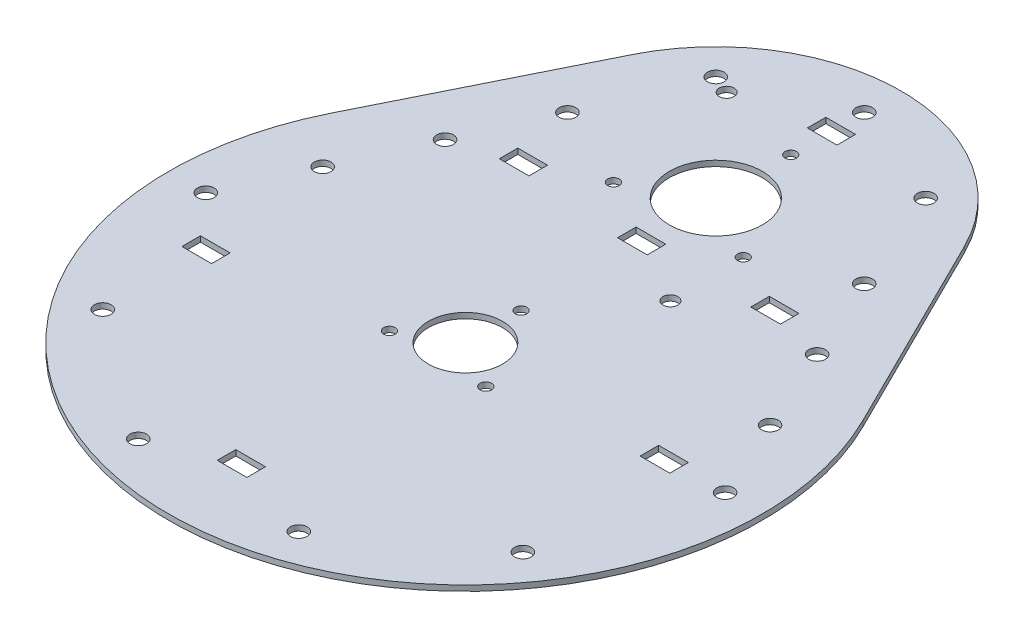
SolidWorks part; units mm, degrees
material "Plain Carbon Steel"
ref_plane "Front Plane" through (0, 0, 0) normal (0, 0, 1) x (1, 0, 0)
ref_plane "Top Plane" through (0, 0, 0) normal (0, 1, 0) x (1, 0, 0)
ref_plane "Right Plane" through (0, 0, 0) normal (1, 0, 0) x (0, 0, -1)
sketch "Sketch1" plane through (0, 0, 0) normal (0, 1, 0) x (1, 0, 0)
  line L0 (0, 67.5) -> (0, 0) construction
  line L1 (12.9904, -7.5) -> (0, 15) construction
  line L2 (0, 15) -> (-12.9904, -7.5) construction
  line L3 (-12.9904, -7.5) -> (12.9904, -7.5) construction
  line L4 (44.7903, 89.7222) -> (71.6645, 35.5556)
  line L5 (-44.7903, 89.7222) -> (-71.6645, 35.5556)
  line L6 (40, 67.5) -> (70, 0) construction
  line L7 (-4, 45) -> (4, 45)
  line L8 (-4, 45) -> (-4, 50)
  line L9 (-4, 50) -> (4, 50)
  line L10 (4, 45) -> (4, 50)
  line L11 (-4, 45) -> (4, 50) construction
  line L12 (-4, 50) -> (4, 45) construction
  line L13 (-40, 67.5) -> (-70, 0) construction
  line L14 (-5.9945, -60.9204) -> (2.0055, -60.9204)
  line L15 (-38.3758, 52.5) -> (-30.3758, 52.5)
  line L16 (-38.3758, 52.5) -> (-38.3758, 47.5)
  line L17 (-38.3758, 47.5) -> (-30.3758, 47.5)
  line L18 (-30.3758, 52.5) -> (-30.3758, 47.5)
  line L19 (-38.3758, 52.5) -> (-30.3758, 47.5) construction
  line L20 (-38.3758, 47.5) -> (-30.3758, 52.5) construction
  line L21 (30.1365, 46.7901) -> (38.1365, 46.7901)
  line L22 (30.1365, 46.7901) -> (30.1365, 51.7901)
  line L23 (30.1365, 51.7901) -> (38.1365, 51.7901)
  line L24 (38.1365, 46.7901) -> (38.1365, 51.7901)
  line L25 (30.1365, 46.7901) -> (38.1365, 51.7901) construction
  line L26 (30.1365, 51.7901) -> (38.1365, 46.7901) construction
  line L27 (-5.9945, -60.9204) -> (-5.9945, -55.9204)
  line L28 (-5.9945, -55.9204) -> (2.0055, -55.9204)
  line L29 (2.0055, -60.9204) -> (2.0055, -55.9204)
  line L30 (50.013, -2.9205) -> (58.013, -2.9205)
  line L31 (50.013, -2.9205) -> (50.013, 2.0795)
  line L32 (50.013, 2.0795) -> (58.013, 2.0795)
  line L33 (58.013, -2.9205) -> (58.013, 2.0795)
  line L34 (-60.6738, -15.7602) -> (-52.6738, -15.7602)
  line L35 (-60.6738, -15.7602) -> (-60.6738, -10.7602)
  line L36 (-60.6738, -10.7602) -> (-52.6738, -10.7602)
  line L37 (-52.6738, -15.7602) -> (-52.6738, -10.7602)
  line L38 (-4.0466, 96.2118) -> (3.9534, 96.2118)
  line L39 (-4.0466, 96.2118) -> (-4.0466, 101.2118)
  line L40 (-4.0466, 101.2118) -> (3.9534, 101.2118)
  line L41 (3.9534, 96.2118) -> (3.9534, 101.2118)
  line L43 (0, 87.7073) -> (-17.5, 57.3964) construction
  line L44 (-17.5, 57.3964) -> (17.5, 57.3964) construction
  line L45 (17.5, 57.3964) -> (0, 87.7073) construction
  circle A0 centre (0, 0) radius 10
  circle A1 centre (0, 0) radius 7.5 construction
  circle A2 centre (-12.9904, -7.5) radius 1.55
  circle A3 centre (12.9904, -7.5) radius 1.55
  circle A4 centre (0, 15) radius 1.55
  arc A6 (-71.6645, 35.5556) -> (71.6645, 35.5556) centre (0, 0) ccw
  circle A7 centre (0, 67.5) radius 12.525
  arc A8 (44.7903, 89.7222) -> (-44.7903, 89.7222) centre (0, 67.5) ccw
  circle A9 centre (0, 0) radius 35 construction
  circle A10 centre (0, 67.5) radius 15 construction
  circle A11 centre (0, 0) radius 45 construction
  circle A12 centre (0, 67.5) radius 22.5 construction
  circle A14 centre (40, 67.5) radius 2.25
  circle A15 centre (70, 0) radius 2.25
  circle A16 centre (56.6312, -41.145) radius 2.25
  circle A17 centre (21.6312, -66.574) radius 2.25
  circle A18 centre (-21.6312, -66.574) radius 2.25
  circle A19 centre (-56.6312, -41.145) radius 2.25
  circle A20 centre (-70, 0) radius 2.25
  circle A21 centre (28.2843, 95.7843) radius 2.25
  circle A22 centre (0, 107.5) radius 2.25
  circle A23 centre (-28.2843, 95.7843) radius 2.25
  circle A24 centre (-40, 67.5) radius 2.25
  circle A25 centre (-50.1535, 44.6547) radius 2.25
  circle A26 centre (-60.3069, 21.8094) radius 2.25
  circle A27 centre (50.1535, 44.6547) radius 2.25
  circle A28 centre (60.3069, 21.8094) radius 2.25
  circle A30 centre (17.8596, -30.1004) radius 2 construction
  circle A31 centre (-23.2495, 26.1622) radius 2 construction
  circle A32 centre (0, 67.5) radius 10.1036 construction
  circle A33 centre (0, 87.7073) radius 1.55
  circle A34 centre (-17.5, 57.3964) radius 1.55
  circle A35 centre (17.5, 57.3964) radius 1.55
  circle A36 centre (0, 67.5) radius 35 construction
  circle A37 centre (-23.2495, 93.6622) radius 2
  circle A38 centre (17.8596, 37.3996) radius 2
  point P11 (0, 21.0074)
  point P21 (0, 47.5)
  point P42 (0, 0)
  point P51 (0, 67.5)
  point P62 (34.1365, 49.2901)
  point P63 (-34.3758, 50)
  dimension "D1" = 20
  dimension "D3" = 3.1
  dimension "D4" = 4.5
  dimension "D5" = 50
  dimension "D6" = 25.05
  dimension "D7" = 70
  dimension "D8" = 30
  dimension "D12" = 90
  dimension "D13" = 45
  dimension "D14" = 40
  dimension "D15" = 80
  dimension "D16" = 4.5
  dimension "D22" = 4
  dimension "D23" = 4
  dimension "D24" = 15
  dimension "D31" = 3.1
  dimension "D32" = 70
  dimension "D33" = 4
  dimension "D34" = 4
  dimension "D35" = 24
  dimension "D36" = 20
  dimension "D9" = 5
  dimension "D10" = 8
  dimension "D11" = 20
  dimension "D17" = 70
  dimension "D26" = 8
  dimension "D27" = 5
  dimension "D28" = 8
  dimension "D29" = 5
  dimension "D30" = 35
  dimension "D20" = 3
  dimension "D21" = 3
  dimension "D18" = 6
  dimension "D19" = 5
extrude "Boss-Extrude1" add sketch "Sketch1" along normal blind 1.5
sketch "Sketch2" plane through (0, 1.5, 0) normal (0, 1, 0) x (1, 0, 0)
  line L0 (-5.5214, 72.0585) -> (-38.6611, 31.9193) construction
  line L1 (5.5214, 72.0585) -> (38.6611, 31.9193) construction
  circle A0 centre (0, 0) radius 50.135 construction
  circle A1 centre (0, 67.5) radius 7.16 construction
  dimension "D1" = 100.27
  dimension "D2" = 14.32
sketch "Sketch3" plane through (0, 1.5, 0) normal (0, 1, 0) x (1, 0, 0)
  circle A0 centre (0, 67.5) radius 9 construction
  circle A2 centre (0, 0) radius 58.5 construction
  dimension "D1" = 18
  dimension "D2" = 117
